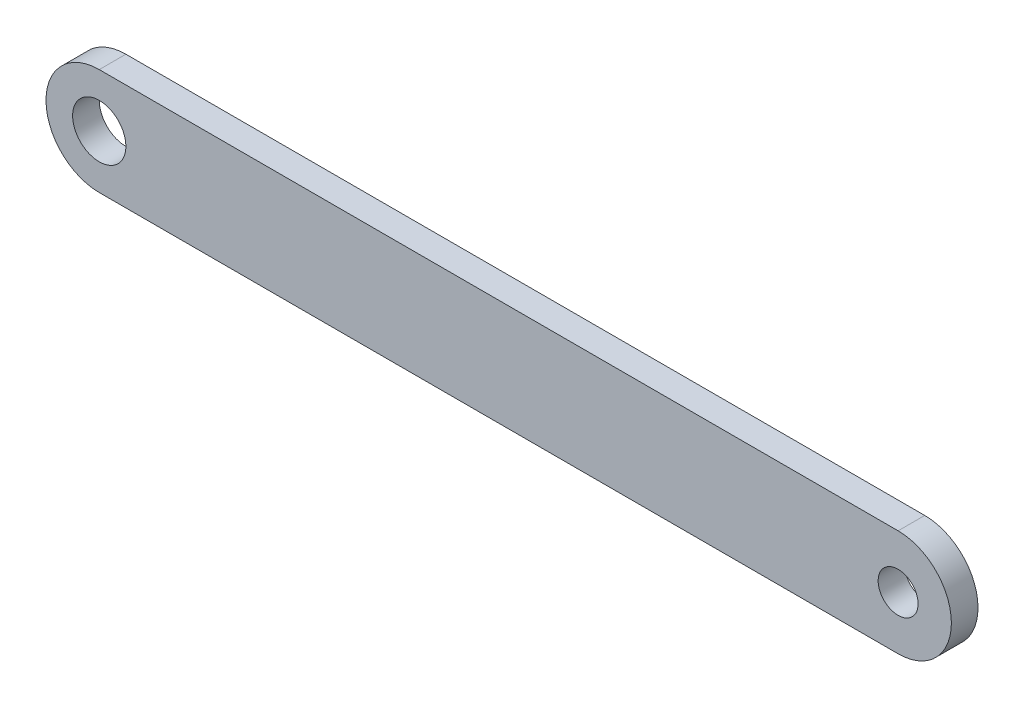
SolidWorks part; units mm, degrees
ref_plane "Front Plane" through (0, 0, 0) normal (0, 0, 1) x (1, 0, 0)
ref_plane "Top Plane" through (0, 0, 0) normal (0, 1, 0) x (1, 0, 0)
ref_plane "Right Plane" through (0, 0, 0) normal (1, 0, 0) x (0, 0, -1)
sketch "Sketch1" plane through (0, 0, 0) normal (0, 0, 1) x (1, 0, 0)
  line L0 (-150, 0) -> (150, 0) construction
  line L1 (-150, 20) -> (150, 20)
  line L2 (-150, -20) -> (150, -20)
  arc A0 (-150, 20) -> (-150, -20) centre (-150, 0) ccw
  arc A1 (150, -20) -> (150, 20) centre (150, 0) ccw
  point P3 (0, 0)
  dimension "D2" = 20
  dimension "D1" = 300
  dimension "D3" = 0
extrude "Boss-Extrude1" add sketch "Sketch1" along normal mid plane 10
sketch "Sketch2" plane through (0, 0, 5) normal (0, 0, 1) x (1, 0, 0)
  circle A0 centre (-150, 0) radius 10
  circle A1 centre (150, 0) radius 7.5
  dimension "D1" = 20
  dimension "D2" = 15
extrude "Cut-Extrude1" cut sketch "Sketch2" against normal through all both
